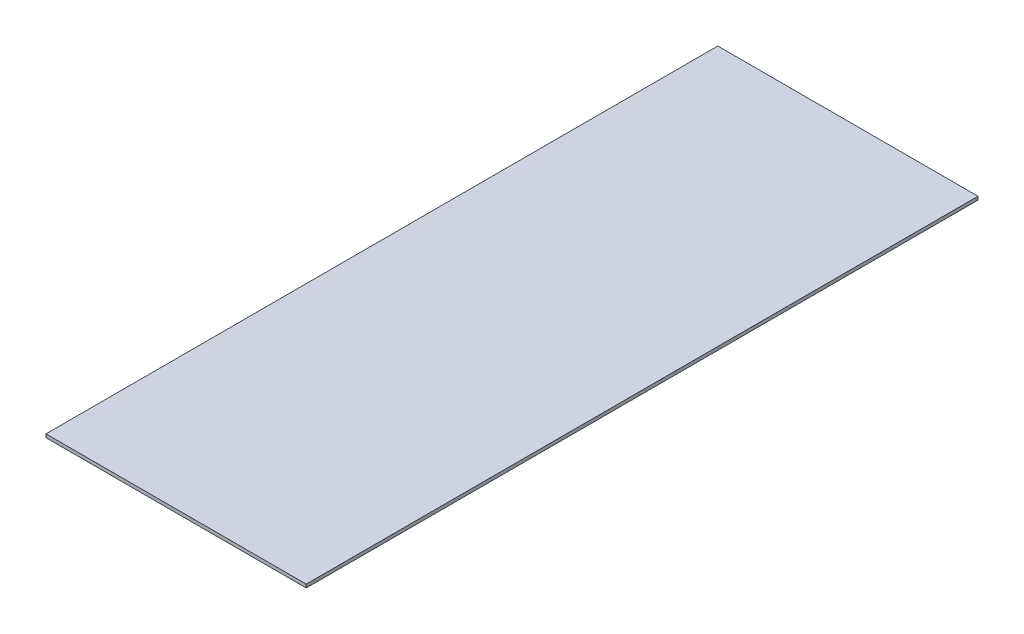
SolidWorks part; units mm, degrees
material "Thornel Mat VMA"
ref_plane "Alzado" through (0, 0, 0) normal (0, 0, 1) x (1, 0, 0)
ref_plane "Planta" through (0, 0, 0) normal (0, 1, 0) x (1, 0, 0)
ref_plane "Vista lateral" through (0, 0, 0) normal (1, 0, 0) x (0, 0, -1)
sketch "Croquis1" plane through (0, 0, 0) normal (0, 1, 0) x (1, 0, 0)
  line L1 (-115.47, 298.1) -> (115.47, 298.1)
  line L2 (-115.47, 298.1) -> (-115.47, -298.1)
  line L3 (-115.47, -298.1) -> (115.47, -298.1)
  line L4 (115.47, 298.1) -> (115.47, -298.1)
  line L5 (-115.47, 298.1) -> (115.47, -298.1) construction
  line L6 (-115.47, -298.1) -> (115.47, 298.1) construction
  point P0 (0, 0)
  dimension "D1" = 230.94
  dimension "D2" = 596.2
extrude "Saliente-Extruir1" add sketch "Croquis1" along normal blind 3
